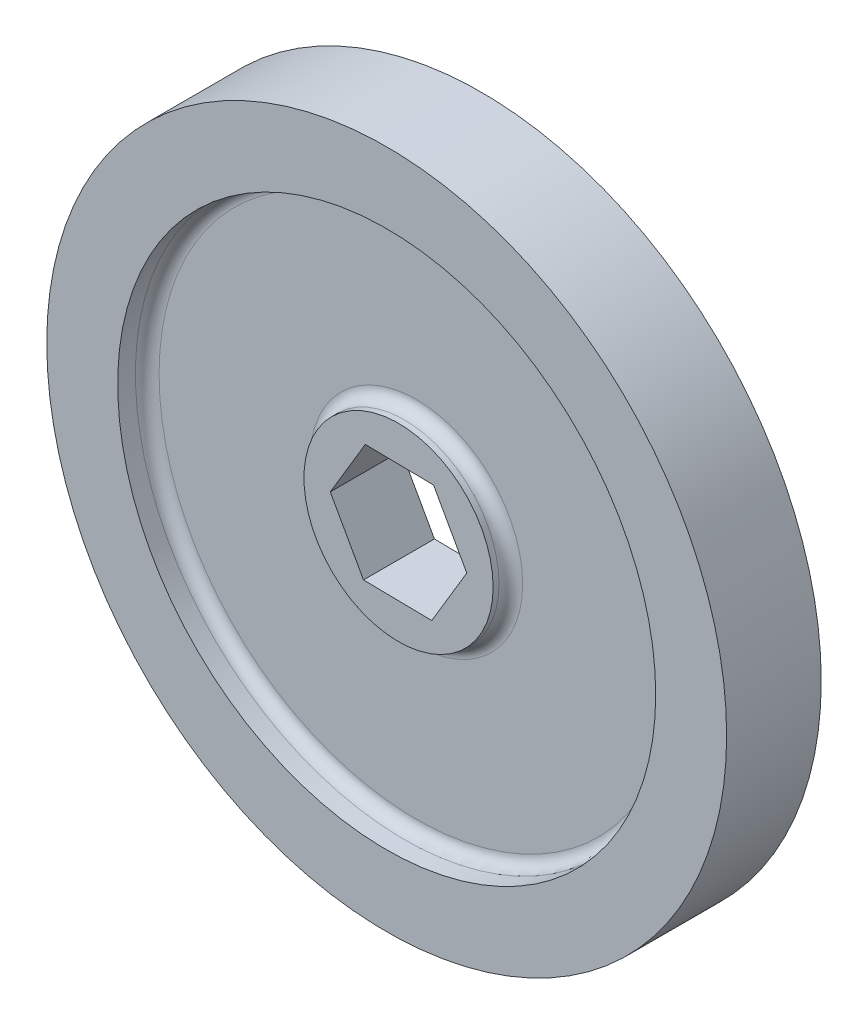
SolidWorks part; units mm, degrees
ref_plane "Front Plane" through (0, 0, 0) normal (0, 0, 1) x (1, 0, 0)
ref_plane "Top Plane" through (0, 0, 0) normal (0, 1, 0) x (1, 0, 0)
ref_plane "Right Plane" through (0, 0, 0) normal (1, 0, 0) x (0, 0, -1)
sketch "Sketch1" plane through (0, 0, 0) normal (0, 0, 1) x (1, 0, 0)
  line L1 (3.5692, -6.405) -> (7.3315, -0.1114)
  line L2 (7.3315, -0.1114) -> (3.7623, 6.2935)
  line L3 (3.7623, 6.2935) -> (-3.5692, 6.405)
  line L4 (-3.5692, 6.405) -> (-7.3315, 0.1114)
  line L5 (-7.3315, 0.1114) -> (-3.7623, -6.2935)
  line L6 (-3.7623, -6.2935) -> (3.5692, -6.405)
  circle A0 centre (0, 0) radius 36.5125
  circle A1 centre (0, 0) radius 6.35 construction
  dimension "D1" = 73.025
  dimension "D2" = 12.7
extrude "Boss-Extrude1" add sketch "Sketch1" along normal blind 10.16
sketch "Sketch2" plane through (0, 0, 10.16) normal (0, 0, 1) x (1, 0, 0)
  circle A0 centre (0, 0) radius 10.16
  circle A1 centre (0, 0) radius 28.8925
  dimension "D1" = 20.32
  dimension "D2" = 57.785
extrude "Cut-Extrude1" cut sketch "Sketch2" against normal blind 3.175
sketch "Sketch3" plane through (0, 0, 0) normal (0, 0, -1) x (-1, 0, 0)
  circle A0 centre (0, 0) radius 28.8925
  circle A1 centre (0, 0) radius 10.16
  dimension "D1" = 57.785
  dimension "D2" = 20.32
extrude "Cut-Extrude2" cut sketch "Sketch3" against normal blind 3.175
sketch "Sketch4" plane through (0, 0, 0) normal (0, 0, -1) x (-1, 0, 0)
  circle A0 centre (0, 0) radius 10.16
extrude "Cut-Extrude3" cut sketch "Sketch4" against normal blind 1.27
sketch "Sketch7" plane through (0, 0, 10.16) normal (0, 0, 1) x (1, 0, 0)
  circle A0 centre (0, 0) radius 10.16
extrude "Cut-Extrude5" cut sketch "Sketch7" against normal blind 1.27
fillet "Fillet1" radius 1.27 4 edges at (-10.16, 0, 3.175) (-28.8925, 0, 3.175) (10.16, 0, 6.985) (28.8925, 0, 6.985)
